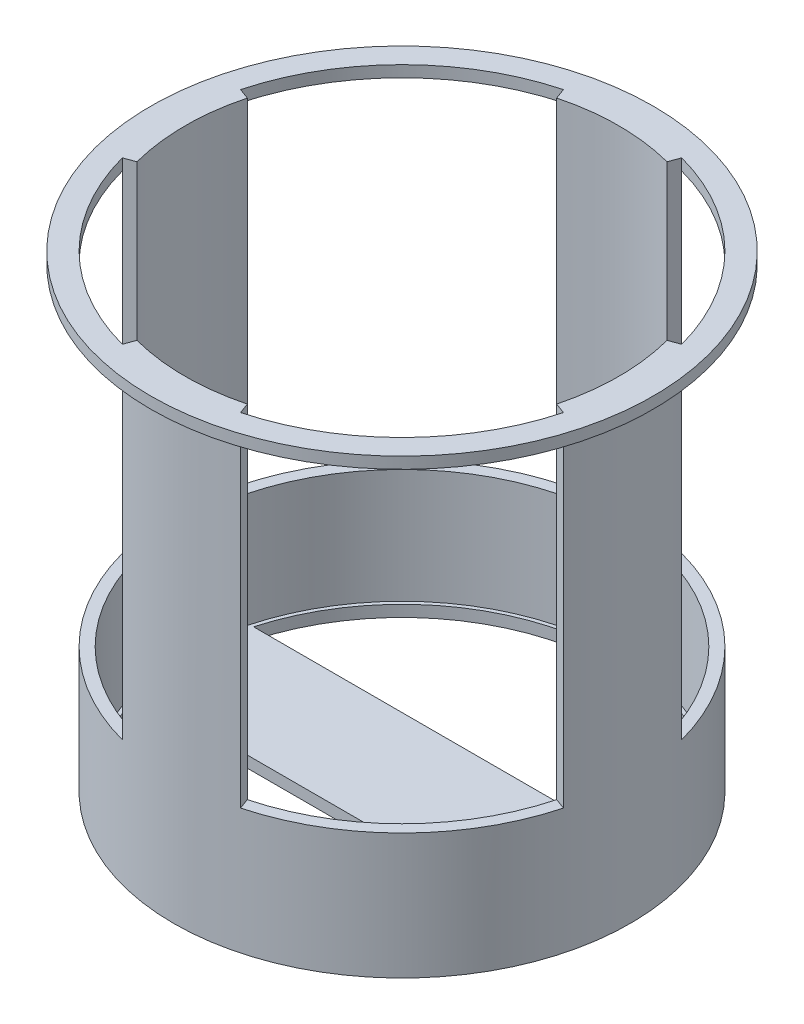
SolidWorks part; units mm, degrees
material "PVC Rigid"
ref_plane "Front Plane" through (0, 0, 0) normal (0, 0, 1) x (1, 0, 0)
ref_plane "Top Plane" through (0, 0, 0) normal (0, 1, 0) x (1, 0, 0)
ref_plane "Right Plane" through (0, 0, 0) normal (1, 0, 0) x (0, 0, -1)
sketch "Sketch1" plane through (0, 0, 0) normal (0, 1, 0) x (1, 0, 0)
  circle A0 centre (0, 0) radius 22
extrude "Boss-Extrude1" add sketch "Sketch1" along normal blind 1
sketch "Sketch2" plane through (0, 1, 0) normal (0, 1, 0) x (1, 0, 0)
  circle A0 centre (0, 0) radius 20
extrude "Cut-Extrude1" cut sketch "Sketch2" against normal blind 1
ref_plane "Plane1" through (0, -40, 0) normal (0, 1, 0) x (1, 0, 0)
sketch "Sketch3" plane through (0, -40, 0) normal (0, 1, 0) x (1, 0, 0)
  circle A0 centre (0, 0) radius 20
extrude "Boss-Extrude2" add sketch "Sketch3" along normal blind 1 separate body
sketch "Sketch4" plane through (0, -39, 0) normal (0, 1, 0) x (1, 0, 0)
  line L2 (0, 0) -> (0, 20) construction
  line L3 (-5.1764, 19.3185) -> (-4.8344, 18.3788)
  line L4 (4.8352, 18.3786) -> (5.1764, 19.3185)
  line L5 (19.3185, 5.1764) -> (18.3788, 4.8344)
  line L6 (18.3786, -4.8352) -> (19.3185, -5.1764)
  line L7 (5.1764, -19.3185) -> (4.8344, -18.3788)
  line L8 (-4.8352, -18.3786) -> (-5.1764, -19.3185)
  line L9 (-19.3185, -5.1764) -> (-18.3788, -4.8344)
  line L10 (-18.3786, 4.8352) -> (-19.3185, 5.1764)
  circle A3 centre (0, 0) radius 20 construction
  arc A4 (0, 20) -> (5.1764, 19.3185) centre (0, 0) cw
  arc A5 (0, 20) -> (-5.1764, 19.3185) centre (0, 0) ccw
  arc A6 (-4.8344, 18.3788) -> (0, 19.004) centre (0, 0) cw
  arc A7 (0, 19.004) -> (4.8352, 18.3786) centre (0, 0) cw
  arc A8 (18.3788, 4.8344) -> (19.004, 0) centre (0, 0) cw
  arc A9 (19.004, 0) -> (18.3786, -4.8352) centre (0, 0) cw
  arc A10 (20, 0) -> (19.3185, 5.1764) centre (0, 0) ccw
  arc A11 (20, 0) -> (19.3185, -5.1764) centre (0, 0) cw
  arc A12 (4.8344, -18.3788) -> (0, -19.004) centre (0, 0) cw
  arc A13 (0, -19.004) -> (-4.8352, -18.3786) centre (0, 0) cw
  arc A14 (0, -20) -> (5.1764, -19.3185) centre (0, 0) ccw
  arc A15 (0, -20) -> (-5.1764, -19.3185) centre (0, 0) cw
  arc A16 (-18.3788, -4.8344) -> (-19.004, 0) centre (0, 0) cw
  arc A17 (-19.004, 0) -> (-18.3786, 4.8352) centre (0, 0) cw
  arc A18 (-20, 0) -> (-19.3185, -5.1764) centre (0, 0) ccw
  arc A19 (-20, 0) -> (-19.3185, 5.1764) centre (0, 0) cw
  point P33 (0, 0)
  dimension "D1" = 4
extrude "Boss-Extrude3" add sketch "Sketch4" along normal up to surface (40 mm away) up to face at (0, 1, 20)
sketch "Sketch5" plane through (0, -39, 0) normal (0, 1, 0) x (1, 0, 0)
  circle A0 centre (0, 0) radius 19.0041
  circle A1 centre (0, 0) radius 20
extrude "Boss-Extrude4" add sketch "Sketch5" along normal blind 10 contours A0 | A1
sketch "Sketch6" plane through (0, -40, 0) normal (0, -1, 0) x (1, 0, 0)
  line L1 (-18, 5) -> (18, 5)
  line L2 (-18, -5) -> (18, -5)
  arc A5 (-18, 5) -> (18, 5) centre (0, 0) cw
  arc A6 (-18, -5) -> (18, -5) centre (0, 0) ccw
  point P4 (0, 0)
  point P10 (0, 5)
  point P16 (0, -5)
extrude "Cut-Extrude2" cut sketch "Sketch6" against normal blind 10 contours A5 L1 | L2 A6
